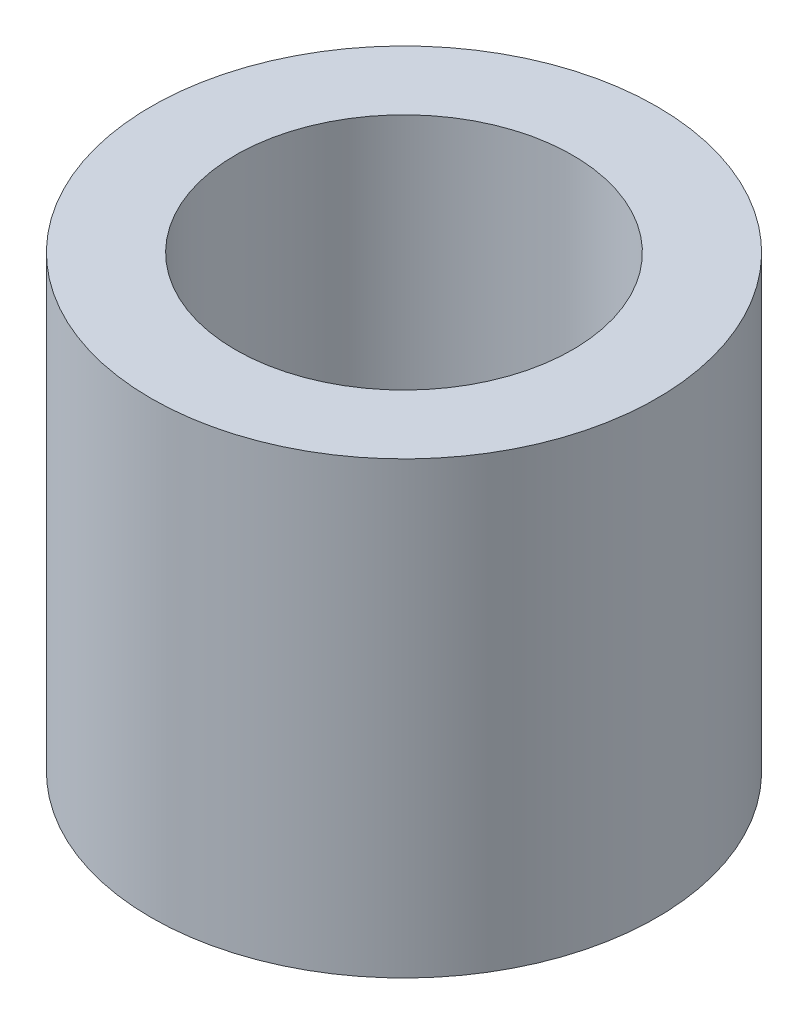
SolidWorks part; units mm, degrees
ref_plane "前视基准面" through (0, 0, 0) normal (0, 0, 1) x (1, 0, 0)
ref_plane "上视基准面" through (0, 0, 0) normal (0, 1, 0) x (1, 0, 0)
ref_plane "右视基准面" through (0, 0, 0) normal (1, 0, 0) x (0, 0, -1)
sketch "草图1" plane through (0, 0, 0) normal (0, 1, 0) x (1, 0, 0)
  circle A0 centre (0, 0) radius 1.5
  circle A1 centre (0, 0) radius 2.25
  dimension "D1" = 3
  dimension "D2" = 4.5
extrude "凸台-拉伸1" add sketch "草图1" along normal blind 4
